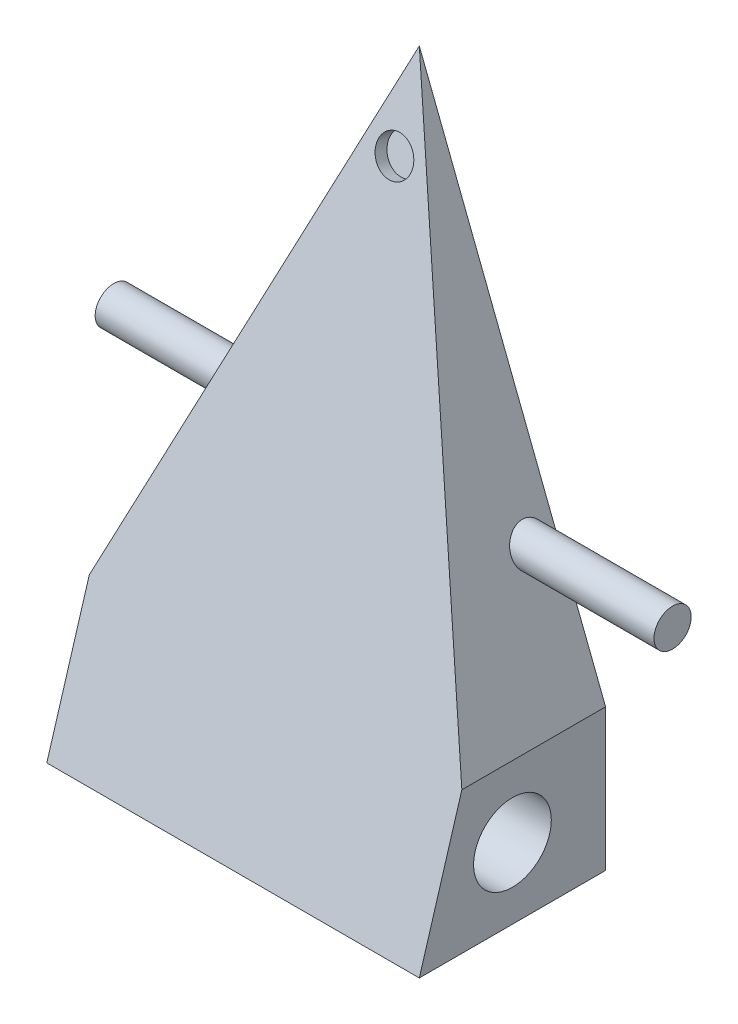
SolidWorks part; units mm, degrees
ref_plane "Front" through (0, 0, 0) normal (0, 0, 1) x (1, 0, 0)
ref_plane "Top" through (0, 0, 0) normal (0, 1, 0) x (1, 0, 0)
ref_plane "Right" through (0, 0, 0) normal (1, 0, 0) x (0, 0, -1)
sketch "Sketch2" plane through (0, 0, 0) normal (1, 0, 0) x (0, 0, -1)
  line L0 (0, -36.5125) -> (0, 63.4875)
  dimension "D1" = 100
extrude "Extrude-Thin1" add sketch "Sketch2" along normal blind 60 thin
sketch "Sketch3" plane through (60, 0, 0) normal (1, 0, 0) x (0, 0, -1)
  line L0 (0, 13.4875) -> (27.5725, 13.4875) construction
  line L1 (0, -36.5125) -> (0, 63.4875) construction
  line L2 (0, 63.4875) -> (0, -36.5125)
  line L3 (0, -36.5125) -> (30, 63.4875)
  line L4 (30, 63.4875) -> (0, 63.4875)
  dimension "D1" = 27.5725
  dimension "D2" = 100
  dimension "D3" = 104.4031
  dimension "D4" = 30
extrude "Cut-Extrude1" cut sketch "Sketch3" against normal blind 60
sketch "Sketch4" plane through (0, 0, -30) normal (0, 0, -1) x (-1, 0, 0)
  line L0 (-30, 63.4875) -> (-60, -13.6841)
  line L1 (-60, 63.4875) -> (0, 63.4875) construction
  line L2 (-60, -36.5125) -> (-60, 63.4875) construction
  line L3 (-60, -13.6841) -> (-60, 63.4875)
  line L4 (-60, 63.4875) -> (-30, 63.4875)
  dimension "D1" = 82.7977
  dimension "D2" = 77.1716
  dimension "D3" = 30
extrude "Cut-Extrude2" cut sketch "Sketch4" against normal blind 60
sketch "Sketch5" plane through (0, 0, -30) normal (0, 0, -1) x (-1, 0, 0)
  line L0 (-30, 63.4875) -> (0, 63.4875)
  line L1 (-30, 63.4875) -> (0, 63.4875) construction
  line L2 (0, 63.4875) -> (0, -13.6841)
  line L3 (0, -36.5125) -> (0, 63.4875) construction
  line L4 (0, -13.6841) -> (-30, 63.4875)
  dimension "D1" = 30
  dimension "D2" = 77.1716
  dimension "D3" = 82.7977
extrude "Cut-Extrude3" cut sketch "Sketch5" against normal blind 60
sketch "Sketch6" plane through (60, 0, 0) normal (1, 0, 0) x (0, 0, -1)
  line L0 (15, -36.5125) -> (15, -13.6841) construction
  line L3 (30, -36.5125) -> (0, -36.5125) construction
  line L4 (6.8485, -13.6841) -> (30, -13.6841) construction
  line L5 (30, -25.0983) -> (0, -25.0983) construction
  line L6 (30, -36.5125) -> (30, -13.6841) construction
  circle A0 centre (15, -25.0983) radius 6.2578
  dimension "D3" = 6.2578
  dimension "D1" = 22.8284
  dimension "D2" = 30
extrude "Cut-Extrude4" cut sketch "Sketch6" against normal through all
sketch "Sketch7" plane through (0, -3.0148, -10.0493) normal (0, 0.2873, 0.9578) x (1, 0, 0)
  line L0 (30, 69.4304) -> (30, -34.9726) construction
  line L2 (60, -34.9726) -> (0, -34.9726) construction
  circle A0 centre (30, 55.4861) radius 3
  dimension "D2" = 3
  dimension "D1" = 104.4031
extrude "Cut-Extrude5" cut sketch "Sketch7" against normal blind 2
sketch "Sketch10" plane through (60, 0, 0) normal (1, 0, 0) x (0, 0, -1)
  circle A0 centre (25.7908, 6.9681) radius 3
  dimension "D1" = 3
extrude "Boss-Extrude1" add sketch "Sketch10" along normal blind 90 from offset 75
